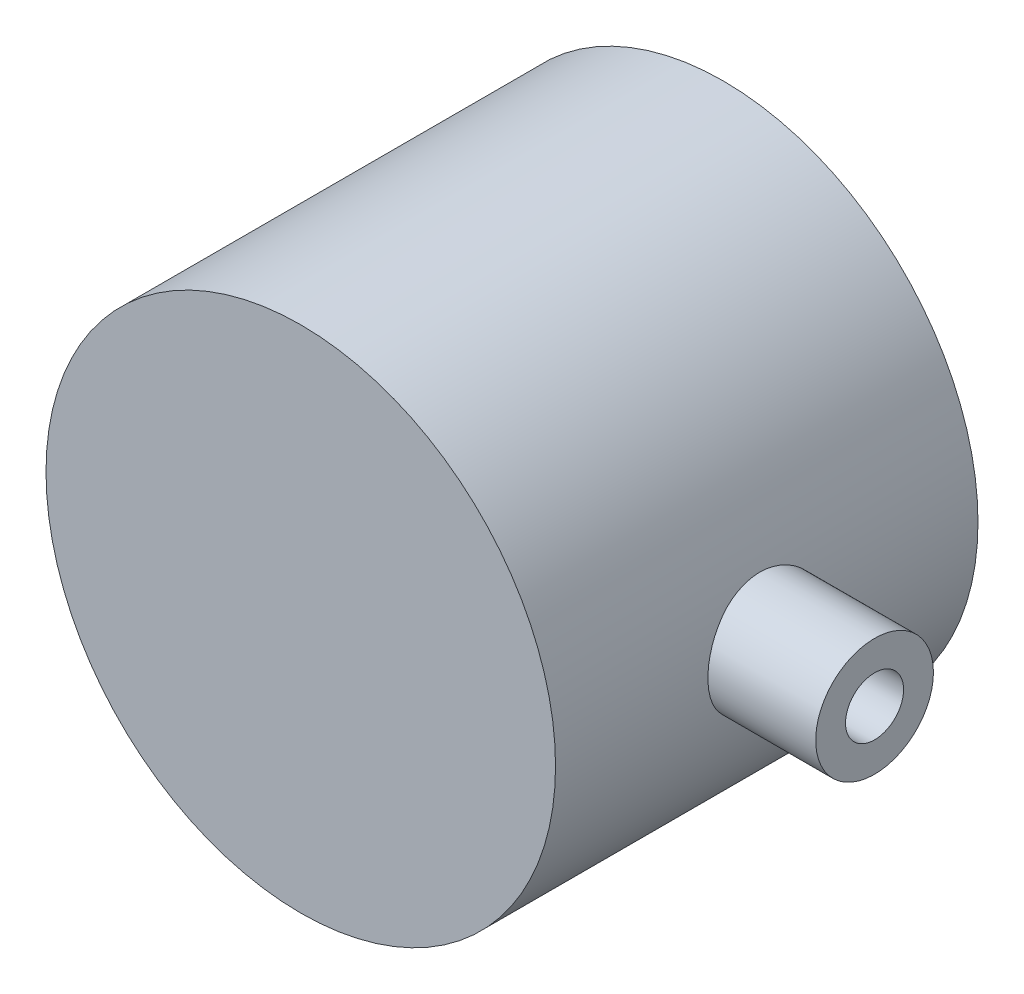
SolidWorks part; units mm, degrees
ref_plane "Ebene vorne" through (0, 0, 0) normal (0, 0, 1) x (1, 0, 0)
ref_plane "Ebene oben" through (0, 0, 0) normal (0, 1, 0) x (1, 0, 0)
ref_plane "Ebene rechts" through (0, 0, 0) normal (1, 0, 0) x (0, 0, -1)
sketch "Sketch1" plane through (0, 0, 0) normal (0, 0, 1) x (1, 0, 0)
  circle A1 centre (0, 0) radius 24.123
  dimension "D3" = 48.246
extrude "Boss-Extrude1" add sketch "Sketch1" along normal blind 35 and the other way blind 5
sketch "Sketch2" plane through (0, 0, 0) normal (1, 0, 0) x (0, 0, -1)
  line L0 (0, 24.123) -> (0, -24.123) construction
  circle A0 centre (-15, 0) radius 3.25
  dimension "D1" = 15
  dimension "D2" = 6.5
extrude "Cut-Extrude2" cut sketch "Sketch2" against normal blind 50 and the other way blind 19.25
sketch "Sketch4" plane through (0, 0, 0) normal (0, 1, 0) x (1, 0, 0)
  line L0 (0, -18.25) -> (0, -11.75) construction
  line L1 (-24.123, 0) -> (24.123, 0) construction
  circle A0 centre (0, -15) radius 3.25
  dimension "D1" = 15
  dimension "D2" = 6.5
extrude "Cut-Extrude3" cut sketch "Sketch4" against normal blind 200
sketch "Sketch5" plane through (0, 0, 0) normal (1, 0, 0) x (0, 0, -1)
  circle A0 centre (-15, 0) radius 11.25
  dimension "D1" = 22.5
extrude "Cut-Extrude8" cut sketch "Sketch5" along normal blind 5.033 from offset 24.123 contours A0 offset against normal yes
sketch "Sketch6" plane through (0, 0, 0) normal (0, 1, 0) x (1, 0, 0)
  line L0 (0, -18.25) -> (0, -11.75) construction
  line L1 (-24.123, -35) -> (24.123, -35) construction
  circle A0 centre (0, -15) radius 11.25
  dimension "D1" = 20
  dimension "D2" = 22.5
extrude "Cut-Extrude9" cut sketch "Sketch6" along normal blind 5.033 from offset 24.123 offset against normal yes
sketch "Sketch7" plane through (0, 0, -5) normal (0, 0, -1) x (-1, 0, 0)
  circle A0 centre (0, 0) radius 17.25
  dimension "D1" = 34.5
extrude "Cut-Extrude10" cut sketch "Sketch7" against normal blind 30
sketch "Sketch8" plane through (0, 0, 0) normal (1, 0, 0) x (0, 0, -1)
  circle A0 centre (-15, 0) radius 2.75
  dimension "D1" = 5.5
extrude "Cut-Extrude11" cut sketch "Sketch8" along normal blind 24.873 from offset 19.25
sketch "Sketch9" plane through (0, 0, 0) normal (1, 0, 0) x (0, 0, -1)
  circle A0 centre (-15, 0) radius 5.575
extrude "Boss-Extrude2" add sketch "Sketch9" along normal blind 11.203 from offset 23.125 separate body
extrude "Cut-Extrude12" cut sketch "Sketch8" along normal blind 50
sketch "Sketch10" plane through (0, 0, 0) normal (1, 0, 0) x (0, 0, -1)
  circle A0 centre (-15, 0) radius 12.25
  dimension "D1" = 24.5
extrude "Cut-Extrude13" cut sketch "Sketch10" along normal blind 4 from offset 24.125 offset against normal yes
sketch "Sketch11" plane through (0, 0, 0) normal (0, 1, 0) x (1, 0, 0)
  circle A0 centre (0, -15) radius 12.25
  dimension "D1" = 24.5
extrude "Cut-Extrude14" cut sketch "Sketch11" along normal blind 4 from offset 24.125
